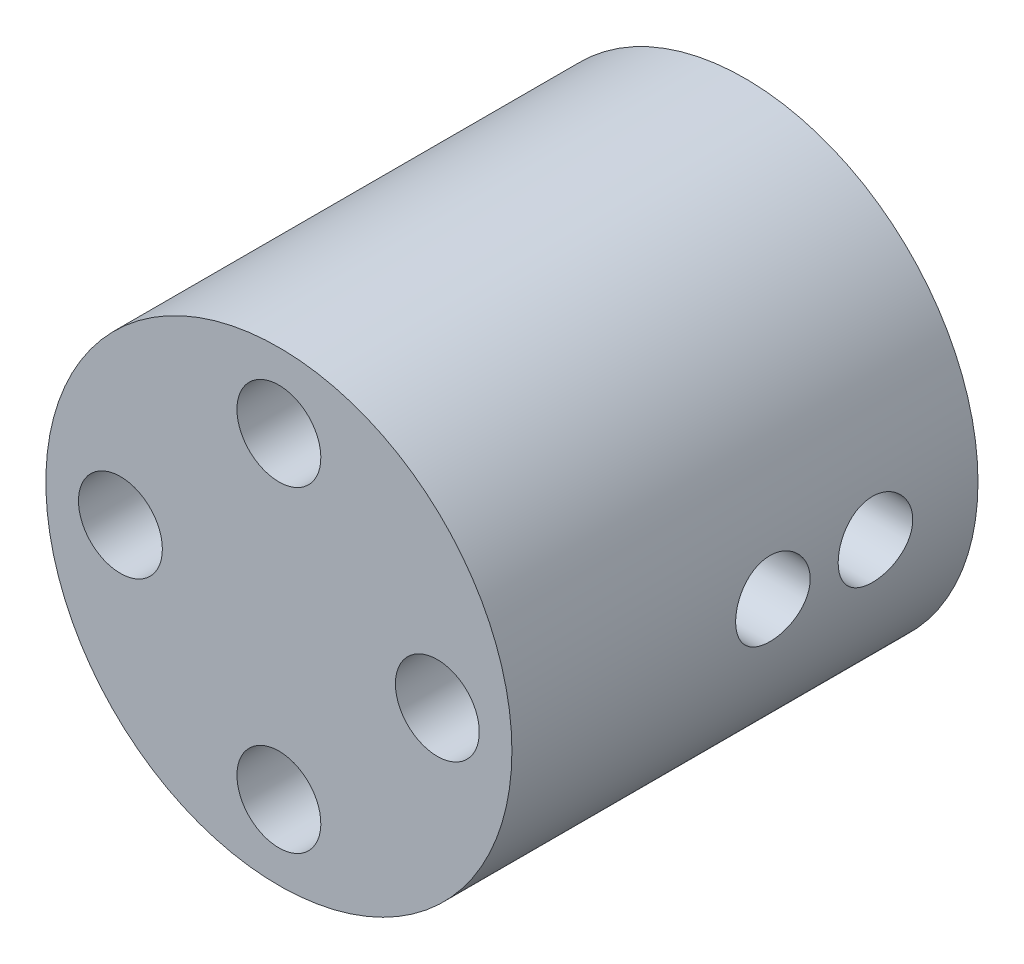
SolidWorks part; units mm, degrees
ref_plane "Front Plane" through (0, 0, 0) normal (0, 0, 1) x (1, 0, 0)
ref_plane "Top Plane" through (0, 0, 0) normal (0, 1, 0) x (1, 0, 0)
ref_plane "Right Plane" through (0, 0, 0) normal (1, 0, 0) x (0, 0, -1)
sketch "Sketch1" plane through (0, 0, 0) normal (0, 0, 1) x (1, 0, 0)
  line L0 (0, 0) -> (2.4, 0) construction
  line L4 (2.5481, -1.8091) -> (2.5481, 1.8091)
  circle A0 centre (0, 0) radius 12.5
  circle A3 centre (0, 0) radius 3.125
  dimension "D1" = 25
  dimension "D2" = 6.25
extrude "Boss-Extrude2" add sketch "Sketch1" along normal blind 25 contours A0
sketch "Sketch13" plane through (0, 0, 25) normal (0, 0, 1) x (1, 0, 0)
  line L0 (-12.5, 0) -> (-4.5, 0) construction
  line L1 (0, 0) -> (12.5, 0) construction
  circle A0 centre (0, 0) radius 12.5 construction
  circle A1 centre (-8.5, 0) radius 2.25
  dimension "D1" = 4.5
  dimension "D2" = 8
extrude "Cut-Extrude7" cut sketch "Sketch13" against normal blind 10
sketch "Sketch14" plane through (0, 0, 0) normal (0, 0, -1) x (-1, 0, 0)
  circle A0 centre (0, 0) radius 3.125 construction
  circle A1 centre (0, 0) radius 3.125
extrude "Cut-Extrude8" cut sketch "Sketch14" against normal blind 3
sketch "Sketch15" plane through (0, 0, 3) normal (0, 0, -1) x (-1, 0, 0)
  line L0 (-2.5481, -1.8091) -> (-2.5481, 1.8091) construction
  line L1 (-2.5481, -1.8091) -> (-2.5481, 1.8091)
  circle A0 centre (0, 0) radius 3.125 construction
  arc A1 (-2.5481, -1.8091) -> (-2.5481, 1.8091) centre (0, 0) ccw
extrude "Cut-Extrude9" cut sketch "Sketch15" against normal blind 12
sketch "Sketch16" plane through (2.5481, 0, 0) normal (-1, 0, 0) x (0, 0, 1)
  line L0 (0, 0) -> (11, 0) construction
  circle A0 centre (11, 0) radius 1.5
  circle A1 centre (5.5, 0) radius 1.5
  dimension "D1" = 3
  dimension "D3" = 3
  dimension "D2" = 11
extrude "Cut-Extrude10" cut sketch "Sketch16" against normal blind 10
sketch "Sketch17" plane through (0, 0, 0) normal (0, 0, -1) x (-1, 0, 0)
  line L0 (-2.5481, 1.8091) -> (-2.5481, -1.8091) construction
  line L1 (-2.5481, 0) -> (-7.5481, 0) construction
  dimension "D1" = 5
pattern_circular "CirPattern1" count 4 over 360 about axis through (0, 0, 0) along (0, 0, 1) of "Cut-Extrude7"
ref_plane "Plane1" through (12.5, 0, 0) normal (1, 0, 0) x (0, 0, -1)
sketch "Sketch18" plane through (12.5, 0, 0) normal (1, 0, 0) x (0, 0, -1)
  circle A0 centre (-11, 0) radius 2
  circle A1 centre (-5.5, 0) radius 2
  dimension "D1" = 4
  dimension "D2" = 4
extrude "Cut-Extrude11" cut sketch "Sketch18" against normal blind 5
